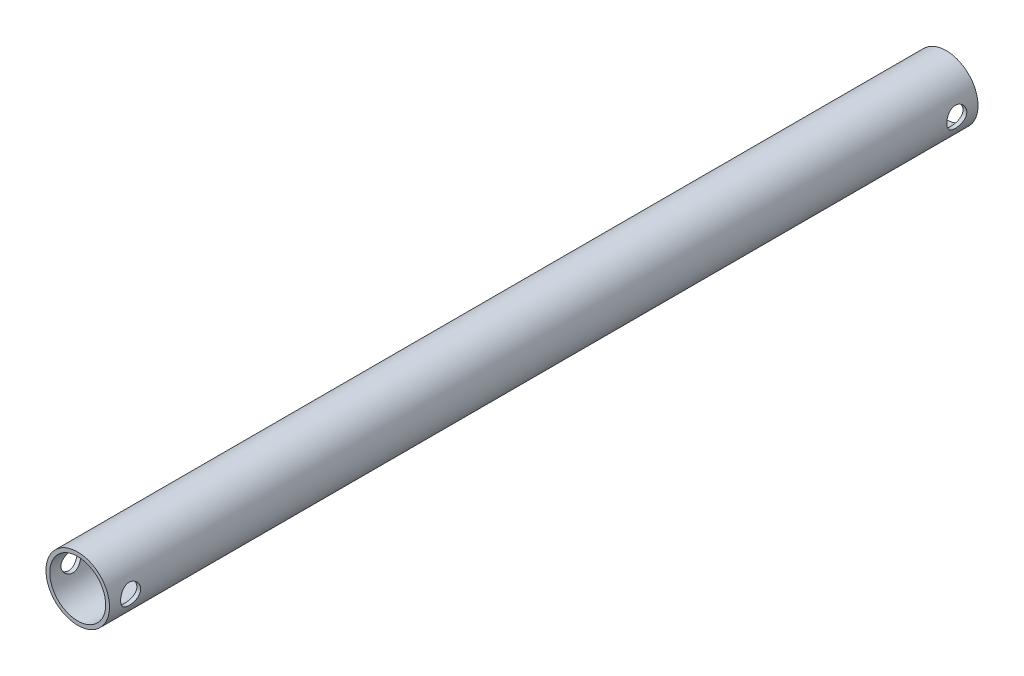
SolidWorks part; units mm, degrees
ref_plane "Front Plane" through (0, 0, 0) normal (0, 0, 1) x (1, 0, 0)
ref_plane "Top Plane" through (0, 0, 0) normal (0, 1, 0) x (1, 0, 0)
ref_plane "Right Plane" through (0, 0, 0) normal (1, 0, 0) x (0, 0, -1)
sketch "Sketch1" plane through (0, 0, 0) normal (0, 0, 1) x (1, 0, 0)
  circle A0 centre (0, 0) radius 9.525
  circle A1 centre (0, 0) radius 8.382
  dimension "D1" = 1.143
extrude "Boss-Extrude1" add sketch "Sketch1" along normal blind 260.35
ref_plane "Plane1" through (9.525, 0, 0) normal (1, 0, 0) x (0, 0, -1)
sketch "Sketch2" plane through (9.525, 0, 0) normal (1, 0, 0) x (0, 0, -1)
  line L0 (0, 0) -> (-6.35, 0) construction
  line L1 (-260.35, 0) -> (-254, 0) construction
  line L2 (-260.35, 9.525) -> (-260.35, -9.525) construction
  circle A0 centre (-254, 0) radius 3
  circle A1 centre (-6.35, 0) radius 3
extrude "Cut-Extrude1" cut sketch "Sketch2" against normal through all
